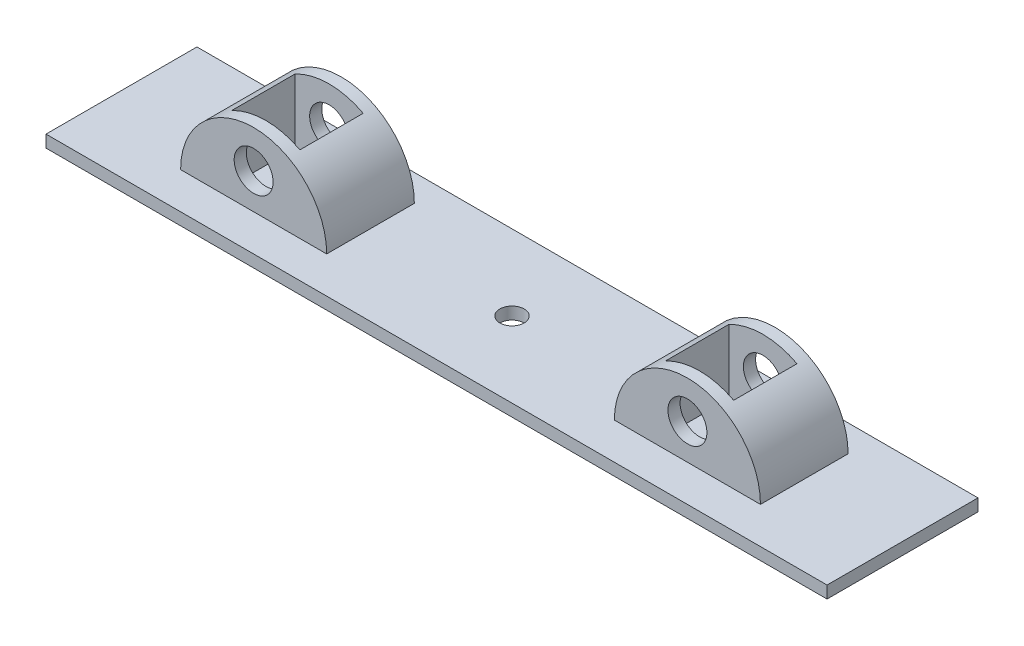
SolidWorks part; units mm, degrees
ref_plane "Front Plane" through (0, 0, 0) normal (0, 0, 1) x (1, 0, 0)
ref_plane "Top Plane" through (0, 0, 0) normal (0, 1, 0) x (1, 0, 0)
ref_plane "Right Plane" through (0, 0, 0) normal (1, 0, 0) x (0, 0, -1)
sketch "Sketch1" plane through (0, 0, 0) normal (0, 1, 0) x (1, 0, 0)
  line L1 (0, 0) -> (160.4, 0)
  line L2 (0, 0) -> (0, 31)
  line L3 (0, 31) -> (160.4, 31)
  line L4 (160.4, 0) -> (160.4, 31)
  circle A0 centre (80.2, 15.5) radius 2.5
  dimension "D3" = 5
  dimension "D1" = 160.4
  dimension "D2" = 31
extrude "Boss-Extrude1" add sketch "Sketch1" along normal blind 2.5
sketch "Sketch2" plane through (0, 0, 0) normal (0, 0, 1) x (1, 0, 0)
  line L0 (0, 2.5) -> (160.4, 2.5) construction
  line L1 (20.1428, 2.5) -> (50.1428, 2.5)
  line L2 (109.2238, 2.5) -> (139.2238, 2.5)
  arc A0 (50.1428, 2.5) -> (20.1428, 2.5) centre (35.1428, 2.5) ccw
  arc A1 (139.2238, 2.5) -> (109.2238, 2.5) centre (124.2238, 2.5) ccw
  circle A2 centre (35.1428, 9.7729) radius 4
  circle A3 centre (124.2238, 9.7729) radius 4
  dimension "D1" = 30
  dimension "D2" = 30
  dimension "D3" = 8
  dimension "D4" = 8
extrude "Boss-Extrude2" add sketch "Sketch2" against normal blind 18 from offset 7.5 offset against normal yes
sketch "Sketch3" plane through (0, 2.5, 0) normal (0, 1, 0) x (1, 0, 0)
  line L0 (50.1428, 25.5) -> (20.1428, 25.5) construction
  line L1 (28.1428, 23) -> (42.1428, 23)
  line L2 (28.1428, 23) -> (28.1428, 10)
  line L3 (28.1428, 10) -> (42.1428, 10)
  line L4 (42.1428, 23) -> (42.1428, 10)
  line L5 (117.2238, 23) -> (131.2238, 23)
  line L6 (117.2238, 23) -> (117.2238, 10)
  line L7 (117.2238, 10) -> (131.2238, 10)
  line L8 (131.2238, 23) -> (131.2238, 10)
  line L9 (50.1428, 25.5) -> (50.1428, 7.5) construction
  line L10 (109.2238, 25.5) -> (139.2238, 25.5) construction
  line L11 (139.2238, 25.5) -> (139.2238, 7.5) construction
  dimension "D1" = 14
  dimension "D2" = 13
  dimension "D3" = 2.5
  dimension "D4" = 8
  dimension "D5" = 14
  dimension "D6" = 13
  dimension "D7" = 2.5
  dimension "D8" = 8
extrude "Cut-Extrude1" cut sketch "Sketch3" along normal blind 18
